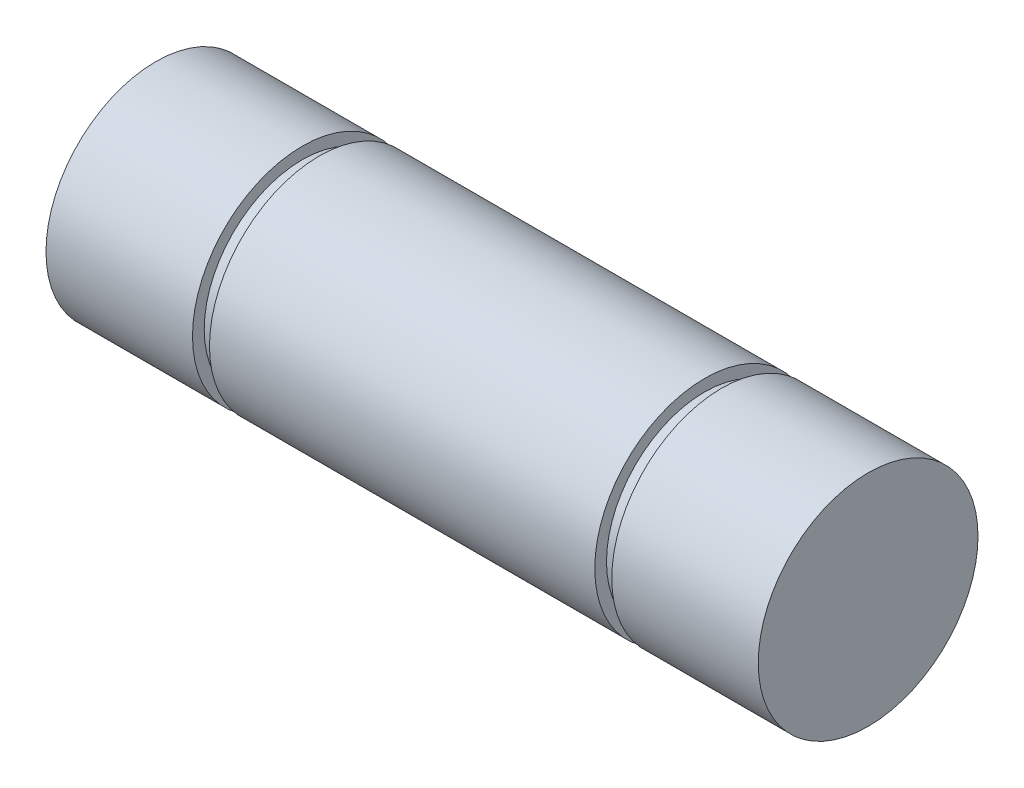
SolidWorks part; units mm, degrees
material "Plain Carbon Steel"
ref_plane "Front" through (0, 0, 0) normal (0, 0, 1) x (1, 0, 0)
ref_plane "Top" through (0, 0, 0) normal (0, 1, 0) x (1, 0, 0)
ref_plane "Right" through (0, 0, 0) normal (1, 0, 0) x (0, 0, -1)
sketch "Sketch2" plane through (0, 0, 0) normal (0, 0, 1) x (1, 0, 0)
  line L0 (439.5414, 279.1725) -> (439.5414, 269.6475) construction
  line L1 (439.5414, 279.1725) -> (439.5414, 269.6475) construction
  line L2 (462.4789, 267.2663) -> (462.4789, 281.5538) construction
  line L3 (470.4164, 269.6475) -> (470.4164, 279.1725) construction
  line L4 (464.0664, 279.1725) -> (464.0664, 269.6475) construction
  line L5 (447.4789, 281.5538) -> (447.4789, 267.2663) construction
  line L6 (445.8914, 269.6475) -> (445.8914, 279.1725) construction
  line L7 (462.4789, 267.2663) -> (462.4789, 281.5538) construction
  line L8 (470.4164, 269.6475) -> (470.4164, 279.1725) construction
  line L9 (464.0664, 279.1725) -> (464.0664, 269.6475) construction
  line L10 (447.4789, 281.5538) -> (447.4789, 267.2663) construction
  line L11 (445.8914, 269.6475) -> (445.8914, 279.1725) construction
  line L12 (439.5414, 274.41) -> (470.4164, 274.41) construction
  line L13 (439.5414, 274.41) -> (439.5414, 279.1725)
  line L14 (439.5414, 279.1725) -> (445.8914, 279.1725)
  line L15 (445.8914, 279.1725) -> (445.8914, 278.6645)
  line L16 (445.8914, 278.6645) -> (446.628, 278.6645)
  line L17 (446.628, 278.6645) -> (446.628, 279.1725)
  line L18 (446.628, 279.1725) -> (463.3298, 279.1725)
  line L19 (454.9789, 267.2663) -> (454.9789, 281.5538) construction
  line L20 (463.3298, 279.1725) -> (463.3298, 278.6645)
  line L21 (463.3298, 278.6645) -> (464.0664, 278.6645)
  line L22 (464.0664, 278.6645) -> (464.0664, 279.1725)
  line L23 (464.0664, 279.1725) -> (470.4164, 279.1725)
  line L24 (470.4164, 279.1725) -> (470.4164, 274.41)
  line L25 (439.5414, 274.41) -> (470.4164, 274.41)
  point P23 (454.9789, 274.41)
  dimension "D1" = 0.7366
  dimension "D2" = 4.7625
  dimension "D3" = 4.2545
revolve "Revolve1" add sketch "Sketch2" angle 360 about L25
